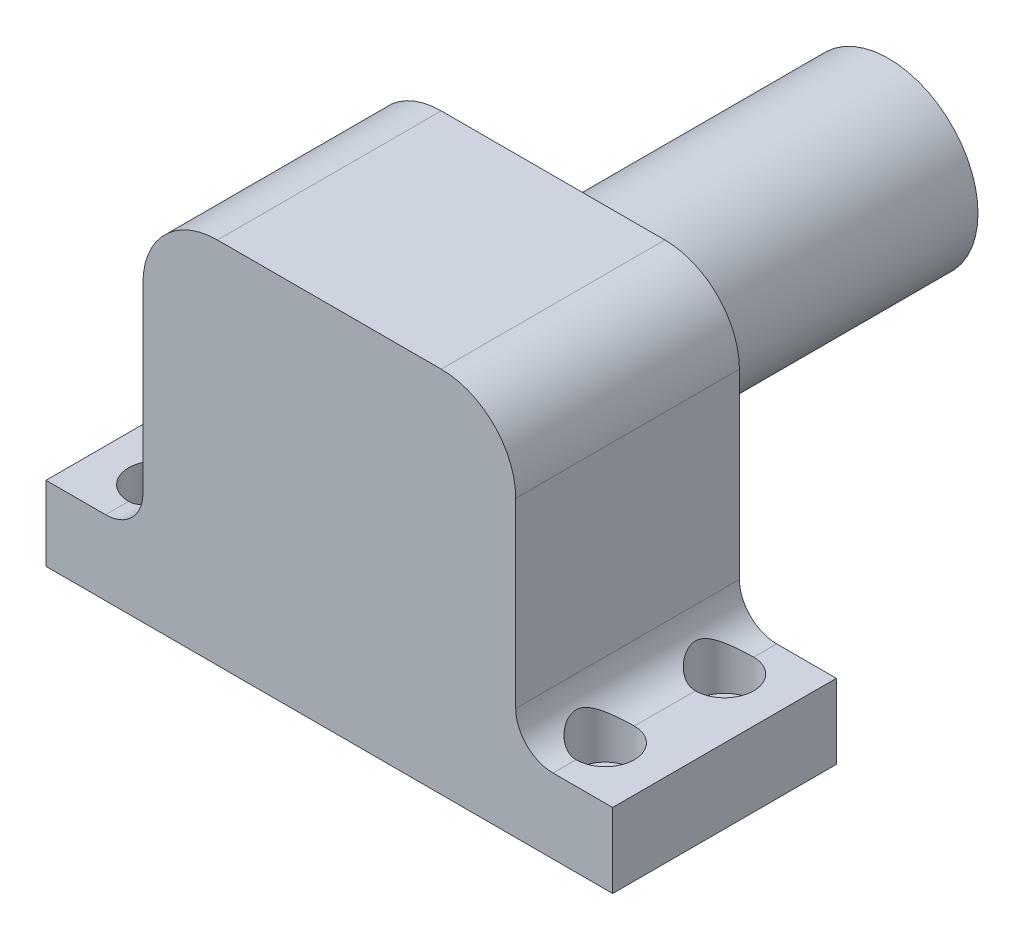
SolidWorks part; units mm, degrees
ref_plane "Front Plane" through (0, 0, 0) normal (0, 0, 1) x (1, 0, 0)
ref_plane "Top Plane" through (0, 0, 0) normal (0, 1, 0) x (1, 0, 0)
ref_plane "Right Plane" through (0, 0, 0) normal (1, 0, 0) x (0, 0, -1)
sketch "Sketch1" plane through (0, 0, 0) normal (0, 0, 1) x (1, 0, 0)
  circle A0 centre (0, 0) radius 12
  dimension "D1" = 24
extrude "Boss-Extrude1" add sketch "Sketch1" along normal blind 45
sketch "Sketch2" plane through (0, 0, 45) normal (0, 0, 1) x (1, 0, 0)
  line L0 (-25, 20.9138) -> (0, 0) construction
  line L1 (-25, 20.9138) -> (25, 20.9138)
  line L2 (-25, 20.9138) -> (-25, -28.4998)
  line L3 (-25, -28.4998) -> (25, -28.4998)
  line L4 (25, 20.9138) -> (25, -28.4998)
  line L5 (0, 0) -> (25, 20.9138) construction
  dimension "D1" = 49.4135
  dimension "D2" = 50
extrude "Boss-Extrude2" add sketch "Sketch2" along normal blind 30
fillet "Fillet1" radius 5 1 edges at (12, 0, 45)
fillet "Fillet2" radius 10 2 edges at (-25, 20.9138, 60) (25, 20.9138, 60)
sketch "Sketch3" plane through (0, 0, 75) normal (0, 0, 1) x (1, 0, 0)
  line L1 (-25, -28.4998) -> (-38, -28.4998)
  line L2 (-25, -28.4998) -> (-25, -18.4998)
  line L3 (-25, -18.4998) -> (-38, -18.4998)
  line L4 (-38, -28.4998) -> (-38, -18.4998)
  line L5 (25, -28.4998) -> (38, -28.4998)
  line L6 (25, -28.4998) -> (25, -18.4998)
  line L7 (25, -18.4998) -> (38, -18.4998)
  line L8 (38, -28.4998) -> (38, -18.4998)
  dimension "D1" = 10
  dimension "D2" = 13
extrude "Boss-Extrude3" add sketch "Sketch3" against normal up to surface (30 mm away) up to face at (17, 0, 45)
fillet "Fillet3" radius 5 2 edges at (25, -18.4998, 60) (-25, -18.4998, 60)
sketch "Sketch4" plane through (0, -28.4998, 0) normal (0, -1, 0) x (1, 0, 0)
  line L0 (-38, 75) -> (38, 75) construction
  line L1 (-30, 68) -> (30, 68) construction
  line L2 (-30, 68) -> (-30, 52) construction
  line L3 (-30, 52) -> (30, 52) construction
  line L4 (30, 68) -> (30, 52) construction
  line L5 (-38, 45) -> (-38, 75) construction
  line L6 (38, 45) -> (38, 75) construction
  line L7 (-38, 45) -> (38, 45) construction
  circle A0 centre (-30, 68) radius 2
  circle A1 centre (-30, 52) radius 2
  circle A2 centre (30, 68) radius 2
  circle A3 centre (30, 52) radius 2
  dimension "D1" = 4
  dimension "D2" = 7
  dimension "D3" = 8
  dimension "D4" = 8
  dimension "D5" = 7
extrude "Cut-Extrude1" cut sketch "Sketch4" against normal through all
sketch "Sketch6" plane through (0, 20.9138, 0) normal (0, 1, 0) x (1, 0, 0)
  circle A0 centre (-30, -52) radius 3.9116
  circle A1 centre (-30, -68) radius 3.9116
  circle A2 centre (30, -52) radius 3.9116
  circle A3 centre (30, -68) radius 3.9116
  dimension "D1" = 7.8232
extrude "Cut-Extrude2" cut sketch "Sketch6" against normal blind 44.4135
